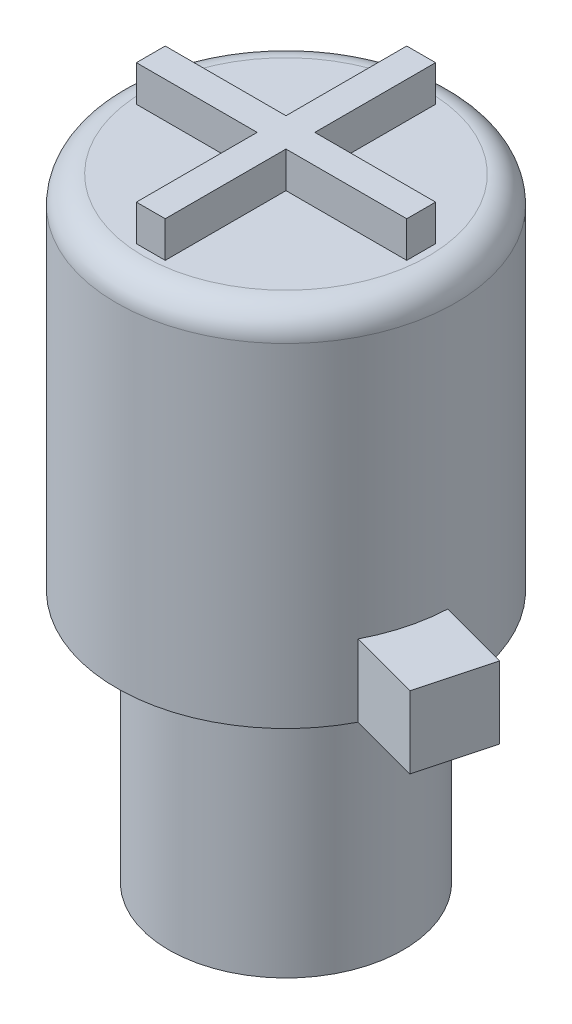
SolidWorks part; units mm, degrees
ref_plane "Front Plane" through (0, 0, 0) normal (0, 0, 1) x (1, 0, 0)
ref_plane "Top Plane" through (0, 0, 0) normal (0, 1, 0) x (1, 0, 0)
ref_plane "Right Plane" through (0, 0, 0) normal (1, 0, 0) x (0, 0, -1)
sketch "Sketch1" plane through (0, 0, 0) normal (0, 1, 0) x (1, 0, 0)
  circle A0 centre (0, 0) radius 3.25
  dimension "D1" = 6.5
extrude "Boss-Extrude1" add sketch "Sketch1" along normal blind 7.018 contours A0
sketch "Sketch2" plane through (0, 0, 0) normal (0, -1, 0) x (1, 0, 0)
  circle A1 centre (0, 0) radius 1.75
  dimension "D1" = 3.5
extrude "Cut-Extrude1" [suppressed] cut sketch "Sketch2" against normal blind 2.5
sketch "Sketch6" plane through (0, 7.018, 0) normal (0, 1, 0) x (1, 0, 0)
  circle A0 centre (0, 0) radius 4.7
  dimension "D1" = 9.4
extrude "Boss-Extrude2" add sketch "Sketch6" along normal blind 10 contours A0
sketch "Sketch7" plane through (0, 17.018, 0) normal (0, 1, 0) x (1, 0, 0)
  line L1 (-0.4, -3.75) -> (0.4, -3.75)
  line L2 (-0.4, -3.75) -> (-0.4, 3.75)
  line L3 (-0.4, 3.75) -> (0.4, 3.75)
  line L4 (0.4, -3.75) -> (0.4, 3.75)
  line L5 (-0.4, -3.75) -> (0.4, 3.75) construction
  line L6 (-0.4, 3.75) -> (0.4, -3.75) construction
  line L7 (-3.75, -0.4) -> (3.75, -0.4)
  line L8 (-3.75, -0.4) -> (-3.75, 0.4)
  line L9 (-3.75, 0.4) -> (3.75, 0.4)
  line L10 (3.75, -0.4) -> (3.75, 0.4)
  line L11 (-3.75, -0.4) -> (3.75, 0.4) construction
  line L12 (-3.75, 0.4) -> (3.75, -0.4) construction
  point P0 (0, 0)
  point P6 (0, 0)
  dimension "D1" = 0.8
  dimension "D2" = 7.5
  dimension "D3" = 7.5
  dimension "D4" = 0.8
sketch "Sketch8" plane through (0, 17.018, 0) normal (0, 1, 0) x (1, 0, 0)
  line L0 (0.4, 3.75) -> (-0.4, 3.75)
  line L1 (-0.4, 3.75) -> (-0.4, 0.4)
  line L2 (-0.4, -3.75) -> (-0.4, 3.75) construction
  line L3 (-3.75, 0.4) -> (3.75, 0.4) construction
  line L4 (-0.4, 0.4) -> (-3.75, 0.4)
  line L5 (-3.75, 0.4) -> (-3.75, -0.4)
  line L6 (-3.75, -0.4) -> (-0.4, -0.4)
  line L7 (-3.75, -0.4) -> (3.75, -0.4) construction
  line L8 (-0.4, -0.4) -> (-0.4, -3.75)
  line L9 (-0.4, -3.75) -> (0.4, -3.75)
  line L10 (0.4, -3.75) -> (0.4, -0.4)
  line L11 (0.4, -3.75) -> (0.4, 3.75) construction
  line L12 (0.4, -0.4) -> (3.75, -0.4)
  line L13 (3.75, -0.4) -> (3.75, 0.4)
  line L14 (3.75, 0.4) -> (0.4, 0.4)
  line L15 (0.4, 0.4) -> (0.4, 3.75)
extrude "Boss-Extrude3" add sketch "Sketch8" along normal blind 1
fillet "Fillet1" radius 0.75 1 edges at (0, 17.018, 4.7)
sketch "Sketch9" plane through (0, 17.018, 0) normal (0, 1, 0) x (1, 0, 0)
  line L1 (-0.4, 3.75) -> (0.4, 3.75)
  line L2 (-0.4, 3.75) -> (-0.4, 0.4)
  line L3 (-0.4, 0.4) -> (0.4, 0.4)
  line L4 (0.4, 3.75) -> (0.4, 0.4)
  line L5 (-0.4, -0.4) -> (0.4, -0.4)
  line L6 (-0.4, -0.4) -> (-0.4, -3.75)
  line L7 (-0.4, -3.75) -> (0.4, -3.75)
  line L8 (0.4, -0.4) -> (0.4, -3.75)
sketch "Sketch10" plane through (0, 7.018, 0) normal (0, -1, 0) x (1, 0, 0)
  line L0 (-4.7, 0) -> (4.7, 0) construction
  line L1 (3.3234, 3.3234) -> (-3.3234, -3.3234) construction
  line L2 (4.5399, 1.2164) -> (-4.5399, -1.2164) construction
  line L3 (4.1695, 2.1691) -> (6.1323, 2.695)
  line L4 (6.1323, 2.695) -> (6.6582, 0.7322)
  line L5 (6.6582, 0.7322) -> (4.6955, 0.2063)
  line L6 (-4.6778, 0.4558) -> (-6.6406, -0.0701)
  line L7 (-6.6406, -0.0701) -> (-5.786, -3.2596)
  line L8 (-5.786, -3.2596) -> (-3.8232, -2.7337)
  arc A0 (-4.6778, 0.4558) -> (-3.8232, -2.7337) centre (0, 0) ccw
  circle A1 centre (0, 0) radius 4.7 construction
  arc A2 (4.6955, 0.2063) -> (4.1695, 2.1691) centre (0, 0) ccw
  dimension "D1" = 45
  dimension "D2" = 30
  dimension "D3" = 1.016
  dimension "D4" = 1.016
  dimension "D5" = 2.032
  dimension "D6" = 1.651
  dimension "D7" = 1.651
  dimension "D8" = 2.032
extrude "Boss-Extrude4" add sketch "Sketch10" against normal blind 2
